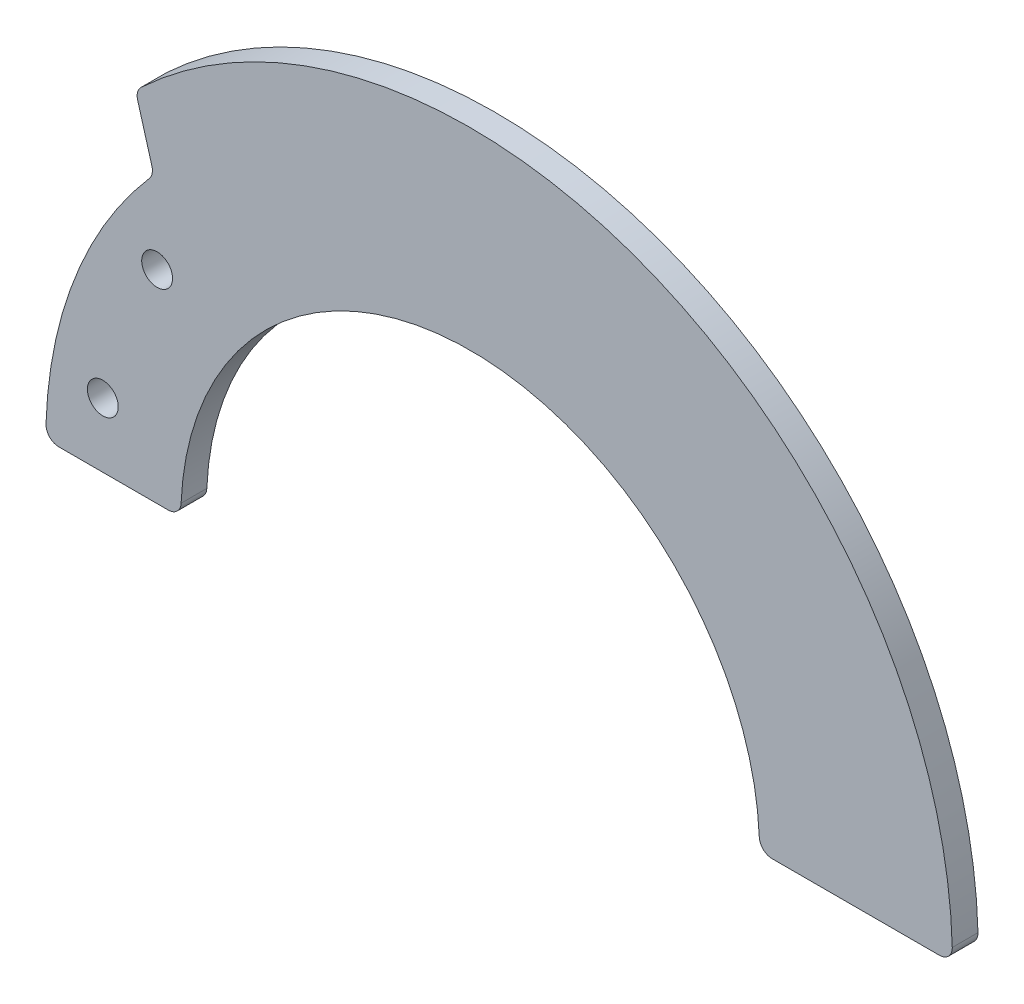
SolidWorks part; units mm, degrees
material "Thornel Mat VMA"
ref_plane "Plan de face" through (0, 0, 0) normal (0, 0, 1) x (1, 0, 0)
ref_plane "Plan de dessus" through (0, 0, 0) normal (0, 1, 0) x (1, 0, 0)
ref_plane "Plan de droite" through (0, 0, 0) normal (1, 0, 0) x (0, 0, -1)
sketch "Esquisse1" plane through (0, 0, 0) normal (0, 0, 1) x (1, 0, 0)
  line L0 (-22.5, 0) -> (-37.5, 0)
  line L1 (22.5, 0) -> (37.5, 0)
  arc A0 (37.5, 0) -> (-37.5, 0) centre (0, 0) ccw
  arc A1 (22.5, 0) -> (-22.5, 0) centre (0, 0) ccw
  arc A2 (28.2, 0) -> (-28.2, 0) centre (0, 0) ccw construction
  dimension "D1" = 75
  dimension "D2" = 56.4
  dimension "D3" = 45
extrude "Boss.-Extru.1" add sketch "Esquisse1" along normal blind 2
hole_wizard "Dégagement M21" positions "Esquisse6" profile "Esquisse4" hole size "M2" standard "DIN"
sketch "Esquisse6" plane through (0, 0, 2) normal (0, 0, 1) x (1, 0, 0)
  line L0 (-37.5, 0) -> (-22.5, 0) construction
  arc A0 (-29, 0) -> (-10.2774, 27.1178) centre (0, 0) cw construction
  point P24 (-28.5657, 5)
  point P26 (-24.3431, 15.7612)
  point P29 (-30, 0)
  dimension "D2" = 29
  dimension "D1" = 11.56
  dimension "D3" = 5
sketch "Esquisse4" plane through (-28.5657, 5, 2) normal (1, 0, 0) x (0, -1, 0)
  line L0 (0, 0) -> (0, 10.721)
  line L1 (0, 10.721) -> (1.2, 10)
  line L2 (1.2, 10) -> (1.2, 0)
  line L5 (1.2, 0) -> (0, 0)
  line L10 (0, 10.721) -> (-1.2, 10) construction
  line L11 (0, -6.35) -> (0, 107.95) construction
  dimension "Diamètre du perçage" = 2.4
  dimension "Profondeur du perçage" = 10
  dimension "Angle de pointe" = 118
sketch "Esquisse7" plane through (0, 0, 2) normal (0, 0, 1) x (1, 0, 0)
  line L0 (-37.5, 0) -> (-22.5, 0) construction
  line L1 (-24.5967, 22) -> (-26.024, 27)
  line L2 (-33, 0) -> (-37.5, 0)
  arc A0 (-33, 0) -> (-24.5967, 22) centre (0, 0) cw
  arc A1 (-37.5, 0) -> (-26.024, 27) centre (0, 0) cw
  dimension "D1" = 33
  dimension "D2" = 5
  dimension "D3" = 22
extrude "Enlèv. mat.-Extru.1" cut sketch "Esquisse7" against normal up to next contours L1 A1 L2 A0
fillet "Congé1" radius 1 6 edges at (37.5, 0, 1) (22.5, 0, 1) (-22.5, 0, 1) (-33, 0, 1) (-26.024, 27, 1) (-24.5967, 22, 1)
